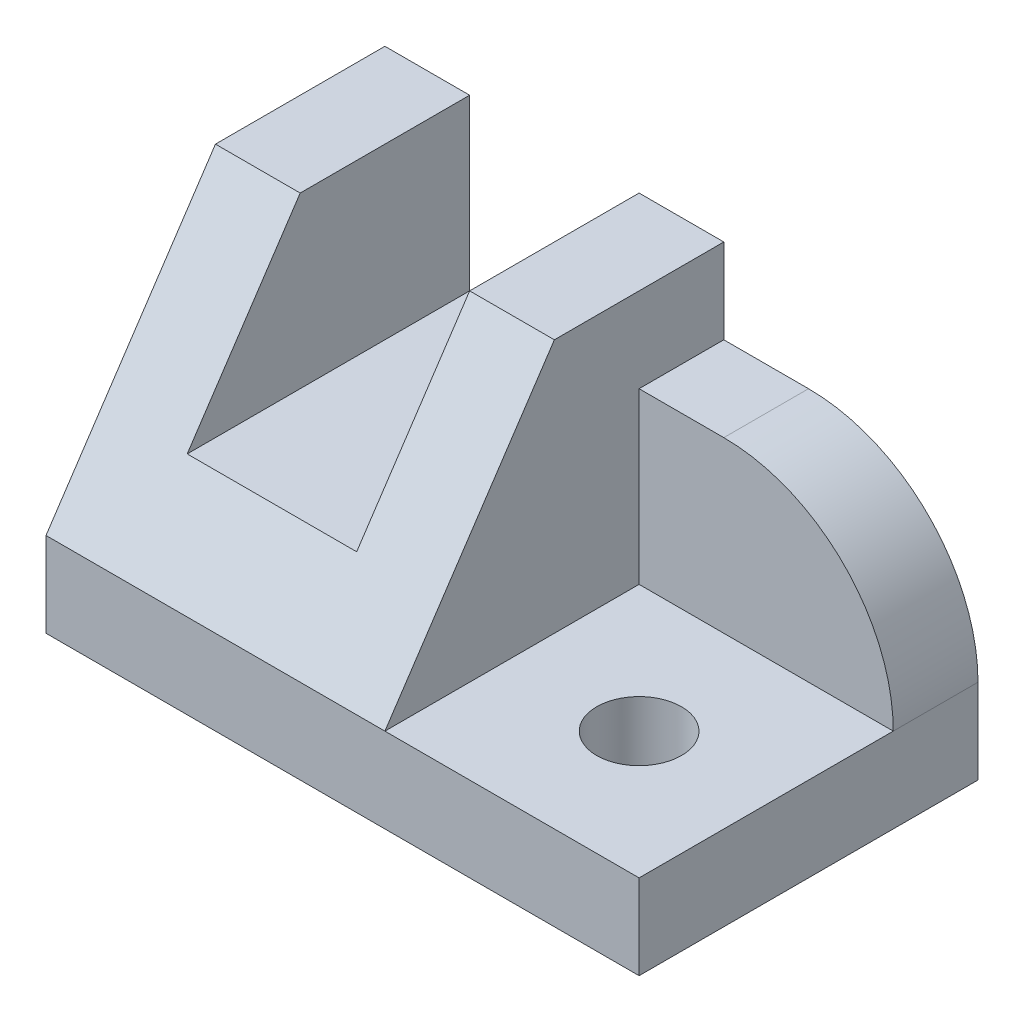
SolidWorks part; units mm, degrees
ref_plane "Front Plane" through (0, 0, 0) normal (0, 0, 1) x (1, 0, 0)
ref_plane "Top Plane" through (0, 0, 0) normal (0, 1, 0) x (1, 0, 0)
ref_plane "Right Plane" through (0, 0, 0) normal (1, 0, 0) x (0, 0, -1)
ref_plane "Plane1" through (0, 0, 0) normal (-1, 0, 0) x (0, -1, 0)
sketch "Sketch1" plane through (0, 0, 0) normal (-1, 0, 0) x (0, -1, 0)
  line L0 (-10, 0) -> (-40, -20)
  line L1 (-40, -20) -> (-10, -20)
  line L2 (-10, -20) -> (-10, 0)
  dimension "D1" = 30
  dimension "Width" = 20
extrude "Boss-Extrude1" add sketch "Sketch1" against normal blind 40
sketch "Sketch2" plane through (0, 0, -20) normal (0, 0, -1) x (-1, 0, 0)
  line L0 (-40, 40) -> (0, 40)
  line L1 (0, 40) -> (0, 10)
  line L2 (0, 10) -> (-40, 10)
  line L3 (-40, 10) -> (-40, 40)
extrude "Boss-Extrude2" add sketch "Sketch2" along normal blind 20
sketch "Sketch3" plane through (40, 0, 0) normal (1, 0, 0) x (0, 0, -1)
  line L0 (40, 10) -> (0, 10)
  line L1 (0, 10) -> (20, 40)
  line L2 (20, 40) -> (40, 40)
  line L3 (40, 40) -> (40, 10)
extrude "Boss-Extrude3" add sketch "Sketch3" along normal blind 30
sketch "Sketch4" plane through (70, 0, 0) normal (1, 0, 0) x (0, 0, -1)
  line L0 (20, 40) -> (0, 10)
  line L1 (0, 10) -> (30, 10)
  line L2 (30, 10) -> (30, 30)
  line L3 (30, 30) -> (40, 30)
  line L4 (40, 30) -> (40, 40)
  line L5 (40, 40) -> (20, 40)
extrude "Cut-Extrude1" cut sketch "Sketch4" against normal blind 30
sketch "Sketch5" plane through (0, 10, 0) normal (0, -1, 0) x (1, 0, 0)
  line L0 (70, 0) -> (70, -40)
  line L1 (70, -40) -> (0, -40)
  line L2 (0, -40) -> (0, 0)
  line L3 (0, 0) -> (70, 0)
extrude "Boss-Extrude4" add sketch "Sketch5" along normal blind 10
sketch "Sketch6" plane through (0, 0, -40) normal (0, 0, -1) x (-1, 0, 0)
  line L0 (-30, 40) -> (-30, 20)
  line L1 (-30, 20) -> (-10, 20)
  line L2 (-10, 20) -> (-10, 40)
  line L3 (-10, 40) -> (-30, 40)
extrude "Cut-Extrude2" cut sketch "Sketch6" against normal through all
hole_wizard "Ø10.0 (10) Diameter Hole1" positions "Sketch8" profile "Sketch7" hole size "Ø10.0" standard "ANSI Metric"
sketch "Sketch8" plane through (0, 0, 0) normal (0, -1, 0) x (-1, 0, 0)
  point P0 (-55, 15)
sketch "Sketch7" plane through (55, 0, -15) normal (1, 0, 0) x (0, 0, -1)
  line L0 (0, 0) -> (0, 40)
  line L1 (0, 40) -> (5, 40)
  line L2 (5, 40) -> (5, 0)
  line L5 (5, 0) -> (0, 0)
  line L11 (0, -6.35) -> (0, 107.95) construction
  dimension "Thru Hole Dia." = 10
  dimension "Thru Hole Depth" = 40
fillet "Fillet1" radius 20 1 edges at (70, 30, -35)
